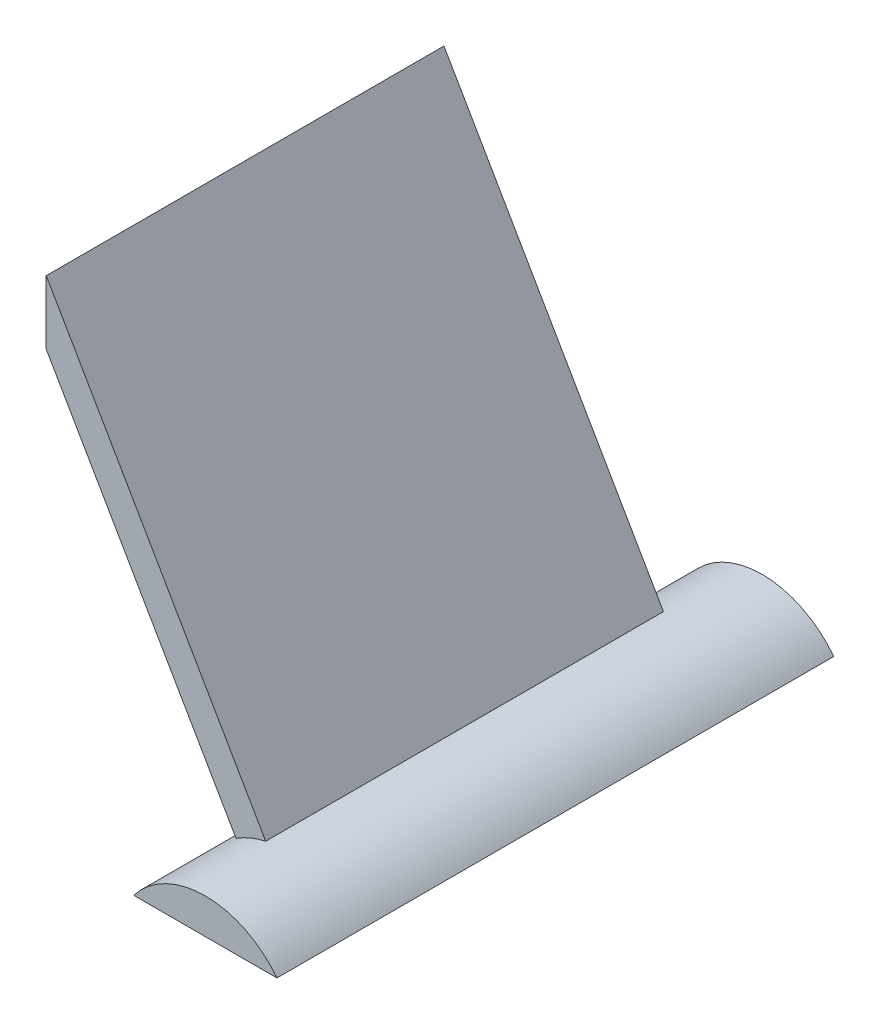
SolidWorks part; units mm, degrees
ref_plane "Front Plane" through (0, 0, 0) normal (0, 0, 1) x (1, 0, 0)
ref_plane "Top Plane" through (0, 0, 0) normal (0, 1, 0) x (1, 0, 0)
ref_plane "Right Plane" through (0, 0, 0) normal (1, 0, 0) x (0, 0, -1)
sketch "Sketch2" plane through (0, 0, 0) normal (0, 0, 1) x (1, 0, 0)
  line L0 (78.74, -4.5312) -> (78.74, 28.318) construction
  line L1 (90.17, 0) -> (67.31, 0)
  line L2 (-33.8874, 5.6388) -> (98.4422, 5.6388) construction
  arc A0 (67.31, 0) -> (78.74, 5.6388) centre (78.74, -8.7651) cw
  arc A1 (90.17, 0) -> (78.74, 5.6388) centre (78.74, -8.7651) ccw
  point P2 (0, 9.1662)
  point P5 (98.4422, 8.8426)
  point P9 (0, 0)
  point P10 (0, 0)
  point P11 (0, 0)
  point P14 (78.74, 0)
  dimension "D2" = 5.6388
  dimension "D1" = 22.86
  dimension "D3" = 78.74
extrude "Boss-Extrude1" add sketch "Sketch2" against normal blind 88.9
ref_plane "Plane1" through (40.64, 0, 0) normal (1, 0, 0) x (0, 0, -1)
ref_plane "Plane2" through (0, 0, -44.45) normal (0, 0, 1) x (1, 0, 0)
sketch "Sketch3" plane through (0, 0, -44.45) normal (0, 0, 1) x (1, 0, 0)
  line L0 (78.74, 0) -> (40.64, 65.9911) construction
  line L1 (67.31, 0) -> (90.17, 0) construction
  line L2 (40.64, -141.9823) -> (40.64, 141.9823) construction
  line L3 (72.8741, 0) -> (40.64, 55.8311) construction
  line L4 (40.64, 65.9911) -> (75.6749, 5.3089)
  line L5 (40.64, 55.8311) -> (70.9425, 3.3457)
  line L6 (40.64, 65.9911) -> (40.64, 55.8311)
  arc A0 (90.17, 0) -> (67.31, 0) centre (78.74, -8.7651) ccw construction
  arc A1 (70.9425, 3.3457) -> (75.6749, 5.3089) centre (80.796, -13.721) cw
  dimension "D1" = 5.08
  dimension "D2" = 30
extrude "Boss-Extrude2" add sketch "Sketch3" along normal blind 31.75 and the other way blind 31.75
ref_plane "Plane3" through (0, 0, 0) normal (1, 0, 0) x (0, 0, -1)
